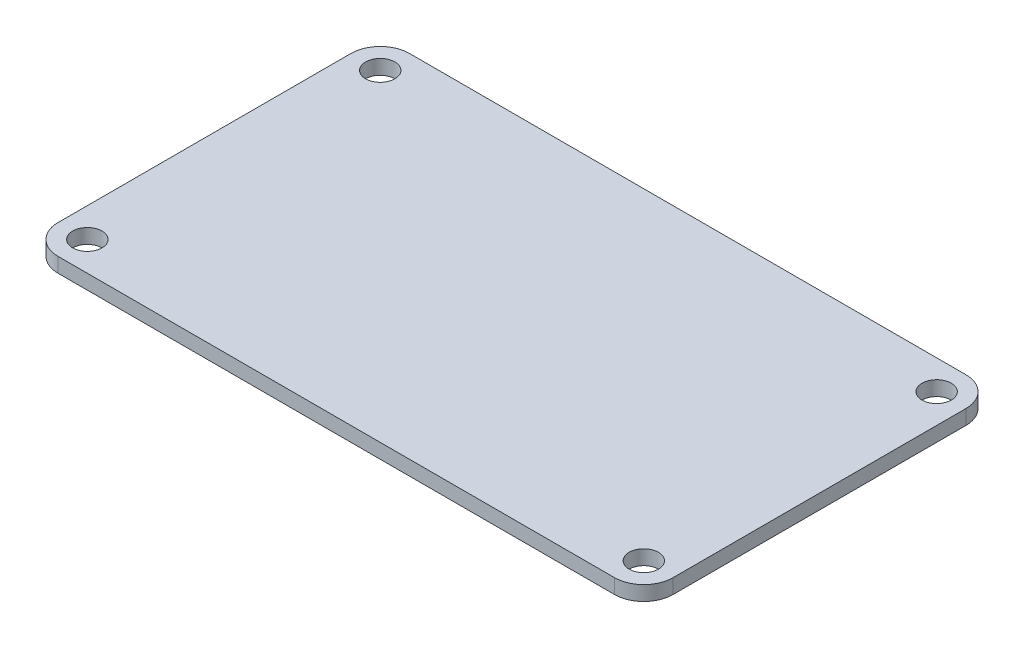
SolidWorks part; units mm, degrees
ref_plane "Front Plane" through (0, 0, 0) normal (0, 0, 1) x (1, 0, 0)
ref_plane "Top Plane" through (0, 0, 0) normal (0, 1, 0) x (1, 0, 0)
ref_plane "Right Plane" through (0, 0, 0) normal (1, 0, 0) x (0, 0, -1)
sketch "Sketch1" plane through (0, 0, 0) normal (0, 1, 0) x (1, 0, 0)
  line L1 (-21, -12) -> (21, -12)
  line L2 (-21, -12) -> (-21, 12)
  line L3 (-21, 12) -> (21, 12)
  line L4 (21, -12) -> (21, 12)
  line L5 (-21, -12) -> (21, 12) construction
  line L6 (-21, 12) -> (21, -12) construction
  point P0 (0, 0)
  dimension "D1" = 24
  dimension "D2" = 42
extrude "Boss-Extrude1" add sketch "Sketch1" along normal blind 1
sketch "Sketch2" plane through (0, 1, 0) normal (0, 1, 0) x (1, 0, 0)
  line L0 (-19, 12) -> (-19, -12) construction
  line L1 (21, 12) -> (-21, 12) construction
  line L2 (-21, -12) -> (21, -12) construction
  line L3 (19, 12) -> (19, -12) construction
  line L4 (-21, 12) -> (-21, -12) construction
  line L5 (21, -12) -> (21, 12) construction
  line L6 (-21, 10) -> (21, 10) construction
  line L7 (-21, -10) -> (21, -10) construction
  circle A0 centre (-19, 10) radius 1
  circle A1 centre (-19, -10) radius 1
  circle A2 centre (19, -10) radius 1
  circle A3 centre (19, 10) radius 1
  dimension "D5" = 2
  dimension "D1" = 2
  dimension "D2" = 2
  dimension "D3" = 2
  dimension "D4" = 2
extrude "Cut-Extrude1" cut sketch "Sketch2" against normal through all
fillet "Fillet1" radius 2 4 edges at (21, 0.5, 12) (21, 0.5, -12) (-21, 0.5, -12) (-21, 0.5, 12)
